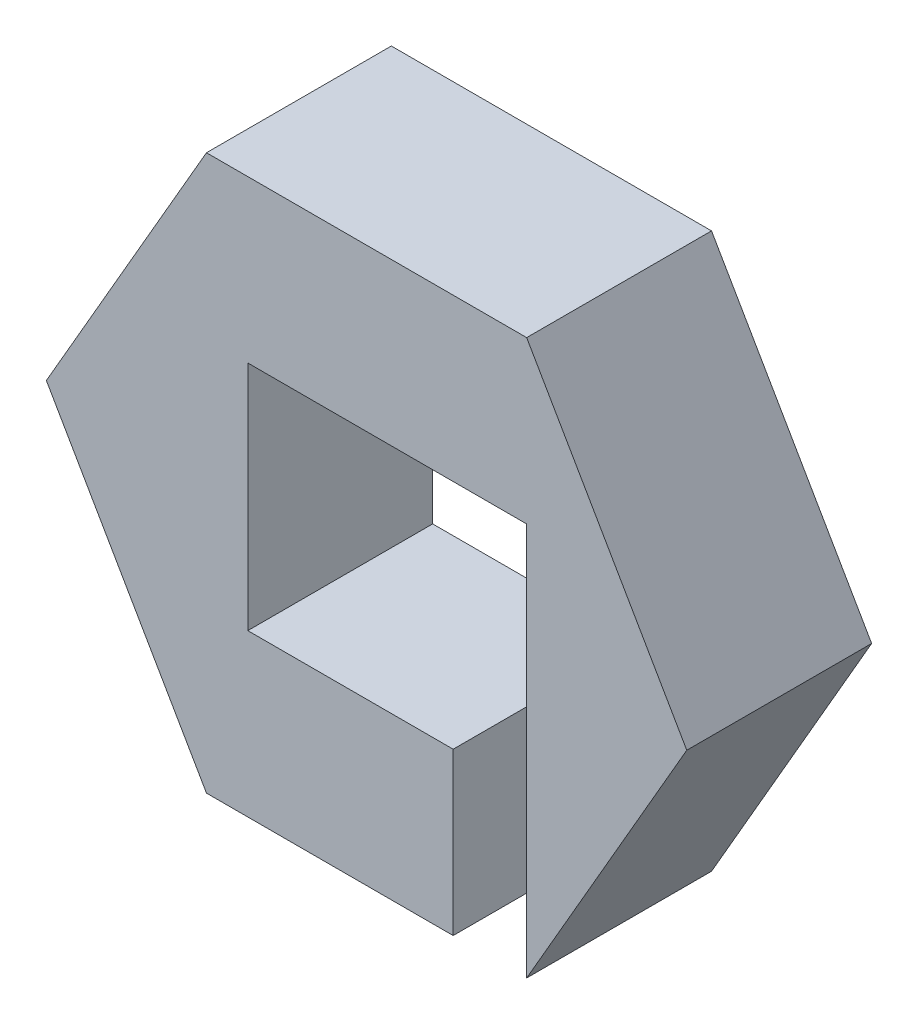
SolidWorks part; units mm, degrees
ref_plane "Front Plane" through (0, 0, 0) normal (0, 0, 1) x (1, 0, 0)
ref_plane "Top Plane" through (0, 0, 0) normal (0, 1, 0) x (1, 0, 0)
ref_plane "Right Plane" through (0, 0, 0) normal (1, 0, 0) x (0, 0, -1)
sketch "Sketch1" plane through (0, 0, 0) normal (0, 0, 1) x (1, 0, 0)
  line L1 (17.3205, 0) -> (8.6603, 15)
  line L2 (8.6603, 15) -> (-8.6603, 15)
  line L3 (-8.6603, 15) -> (-17.3205, 0)
  line L4 (-17.3205, 0) -> (-8.6603, -15)
  line L5 (-8.6603, -15) -> (8.6603, -15)
  line L6 (8.6603, -15) -> (17.3205, 0)
  circle A0 centre (0, 0) radius 15 construction
  dimension "D1" = 30
extrude "Boss-Extrude1" add sketch "Sketch1" along normal blind 10
sketch "Sketch2" plane through (0, 0, 10) normal (0, 0, 1) x (1, 0, 0)
  line L1 (-6.4239, 6.2695) -> (6.4239, 6.2695)
  line L2 (-6.4239, 6.2695) -> (-6.4239, -6.2695)
  line L3 (-6.4239, -6.2695) -> (6.4239, -6.2695)
  line L4 (6.4239, 6.2695) -> (6.4239, -6.2695)
  line L5 (-6.4239, 6.2695) -> (6.4239, -6.2695) construction
  line L6 (-6.4239, -6.2695) -> (6.4239, 6.2695) construction
  point P0 (0, 0)
extrude "Cut-Extrude1" cut sketch "Sketch2" against normal through all
sketch "Sketch3" plane through (0, -15, 0) normal (0, -1, 0) x (1, 0, 0)
  line L0 (-8.6603, 0) -> (8.6603, 0) construction
  line L1 (8.6603, 10) -> (4.6847, 10)
  line L2 (8.6603, 10) -> (8.6603, 0)
  line L3 (8.6603, 0) -> (4.6847, 0)
  line L4 (4.6847, 10) -> (4.6847, 0)
extrude "Cut-Extrude3" cut sketch "Sketch3" against normal up to vertex
